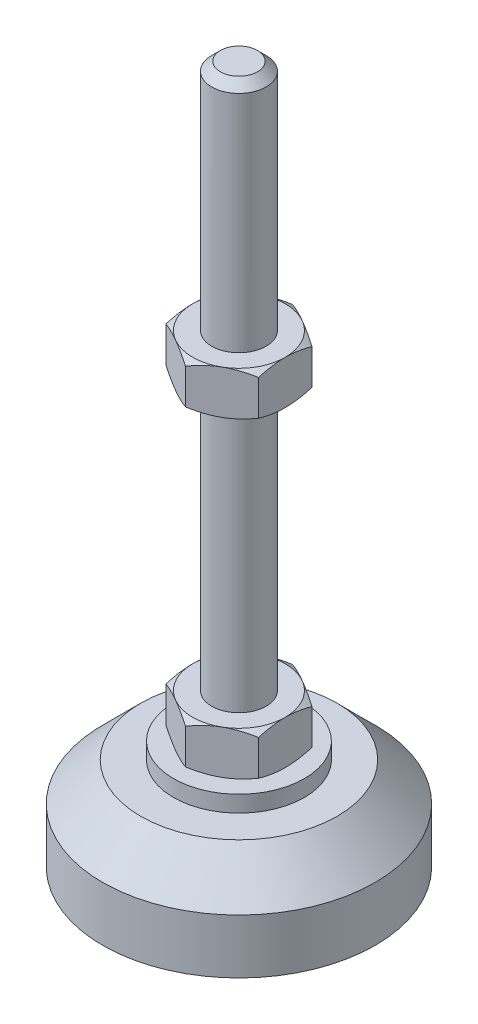
SolidWorks part; units mm, degrees
ref_plane "Спереди" through (0, 0, 0) normal (0, 0, 1) x (1, 0, 0)
ref_plane "Сверху" through (0, 0, 0) normal (0, 1, 0) x (1, 0, 0)
ref_plane "Справа" through (0, 0, 0) normal (1, 0, 0) x (0, 0, -1)
sketch "Эскиз1" plane through (0, 0, 0) normal (0, 0, 1) x (1, 0, 0)
  line L0 (0, 0) -> (-25, 0)
  line L3 (-25, 0) -> (-25, 10)
  line L5 (-12, 20) -> (-5, 20)
  line L12 (-5, 28) -> (-5, 126.4)
  line L13 (-5, 126.4) -> (-3.4, 128)
  line L14 (-3.4, 128) -> (0, 128)
  line L15 (0, 128) -> (0, 0) construction
  line L16 (-5, 20) -> (0, 20) construction
  line L17 (0, 0) -> (0, 128)
  line L18 (0, 0) -> (0, -7.9595) construction
  line L19 (-5, 28) -> (-5, 20)
  line L20 (-12, 20) -> (-12, 17)
  line L21 (-12, 17) -> (-18, 17)
  line L22 (-18, 17) -> (-25, 10)
  point P8 (-5, 77.2)
  point P23 (-8.5, 20)
  dimension "D1" = 10
  dimension "D2" = 20
  dimension "D3" = 8
  dimension "D4" = 50
  dimension "D5" = 5
  dimension "D6" = 1.6
  dimension "D7" = 45
  dimension "D8" = 24
  dimension "D10" = 100
  dimension "D11" = 10
  dimension "D12" = 45
  dimension "D13" = 3
revolve "Повернуть1" add sketch "Эскиз1" angle 360 about L17
sketch "Эскиз2" plane through (0, 20, 0) normal (0, 1, 0) x (1, 0, 0)
  line L1 (0, 9.815) -> (-8.5, 4.9075)
  line L2 (-8.5, 4.9075) -> (-8.5, -4.9075)
  line L3 (-8.5, -4.9075) -> (0, -9.815)
  line L4 (0, -9.815) -> (8.5, -4.9075)
  line L5 (8.5, -4.9075) -> (8.5, 4.9075)
  line L6 (8.5, 4.9075) -> (0, 9.815)
  circle A0 centre (0, 0) radius 8.5 construction
  dimension "D1" = 17
extrude "Бобышка-Вытянуть1" add sketch "Эскиз2" along normal up to vertex (8 mm away) up to point (-5, 28, 0)
ref_plane "Плоскость1" through (0, 77.2, 0) normal (0, 1, 0) x (1, 0, 0)
sketch "Эскиз3" plane through (0, 77.2, 0) normal (0, 1, 0) x (1, 0, 0)
  line L6 (8.5, 4.9075) -> (0, 9.815)
  line L7 (0, 9.815) -> (-8.5, 4.9075)
  line L8 (-8.5, 4.9075) -> (-8.5, -4.9075)
  line L9 (-8.5, -4.9075) -> (0, -9.815)
  line L10 (0, -9.815) -> (8.5, -4.9075)
  line L11 (8.5, -4.9075) -> (8.5, 4.9075)
  line L12 (8.5, 4.9075) -> (0, 9.815)
  line L13 (0, 9.815) -> (-8.5, 4.9075)
  line L14 (-8.5, 4.9075) -> (-8.5, -4.9075)
  line L15 (-8.5, -4.9075) -> (0, -9.815)
  line L16 (0, -9.815) -> (8.5, -4.9075)
  line L17 (8.5, -4.9075) -> (8.5, 4.9075)
  dimension "D1" = 0
extrude "Бобышка-Вытянуть2" add sketch "Эскиз3" along normal blind 8
sketch "Эскиз4" plane through (0, 0, 0) normal (0, 0, 1) x (1, 0, 0)
  line L0 (-8.5, 85.2) -> (-15.4282, 81.2)
  line L1 (-15.4282, 81.2) -> (-15.4282, 85.2)
  line L2 (-15.4282, 85.2) -> (-8.5, 85.2)
  line L3 (-15.4282, 81.2) -> (-8.5, 77.2)
  line L4 (50, 77.2) -> (-50, 77.2) construction
  line L5 (-8.5, 77.2) -> (-15.4282, 77.2)
  line L6 (-15.4282, 77.2) -> (-15.4282, 81.2)
  line L7 (-8.5, 85.2) -> (-8.5, 77.2) construction
  line L8 (-8.5, 28) -> (-15.4282, 28)
  line L9 (-15.4282, 28) -> (-15.4282, 24)
  line L10 (-15.4282, 24) -> (-8.5, 28)
  line L11 (-8.5, 20) -> (-15.4282, 24)
  line L12 (-15.4282, 24) -> (-15.4282, 20)
  line L13 (-15.4282, 20) -> (-8.5, 20)
  line L14 (0, 128) -> (0, 96.3793) construction
  dimension "D1" = 30
  dimension "D2" = 30
revolve "Вырез-Повернуть2" cut sketch "Эскиз4" angle 360 about L14
